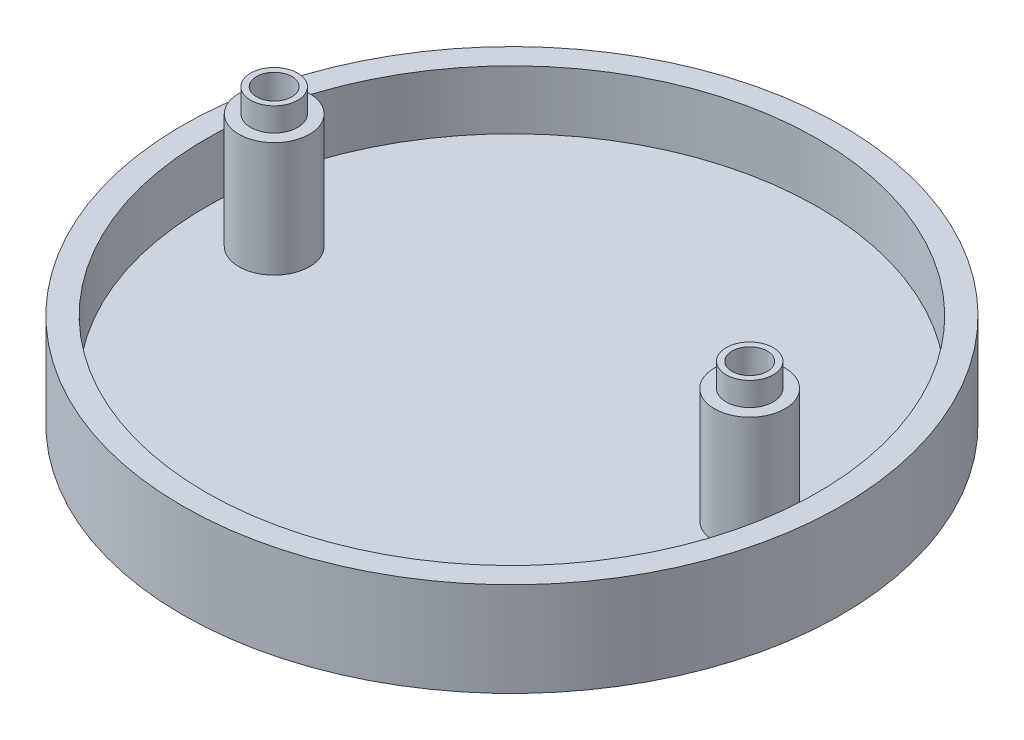
SolidWorks part; units mm, degrees
ref_plane "Front Plane" through (0, 0, 0) normal (0, 0, 1) x (1, 0, 0)
ref_plane "Top Plane" through (0, 0, 0) normal (0, 1, 0) x (1, 0, 0)
ref_plane "Right Plane" through (0, 0, 0) normal (1, 0, 0) x (0, 0, -1)
sketch "Sketch1" plane through (0, 0, 0) normal (0, 1, 0) x (1, 0, 0)
  circle A0 centre (0, 0) radius 28
  circle A1 centre (0, 0) radius 26
  dimension "D1" = 56
  dimension "D2" = 52
extrude "Boss-Extrude1" add sketch "Sketch1" along normal blind 8
sketch "Sketch3" plane through (0, 0, 0) normal (0, 1, 0) x (1, 0, 0)
  circle A0 centre (0, 0) radius 24
extrude "Boss-Extrude2" add sketch "Sketch3" along normal blind 3
sketch "Sketch5" plane through (0, 3, 0) normal (0, 1, 0) x (1, 0, 0)
  line L0 (0, 0) -> (-20.2, 0) construction
  line L1 (0, -4.4) -> (0, 4.4) construction
  circle A0 centre (-20.2, 0) radius 2
  circle A1 centre (20.2, 0) radius 2
  dimension "D2" = 4
  dimension "D1" = 20.2
extrude "Boss-Extrude3" add sketch "Sketch5" along normal blind 11.75 and the other way blind 2.5
sketch "Sketch10" plane through (0, 0, 0) normal (0, -1, 0) x (-1, 0, 0)
  circle A0 centre (0, 0) radius 28
extrude "Boss-Extrude4" add sketch "Sketch10" against normal up to surface (3 mm away) up to face at (0, 3, 24)
sketch "Sketch16" plane through (0, 3, 0) normal (0, 1, 0) x (1, 0, 0)
  line L0 (0, -4.4) -> (0, 4.4) construction
  circle A0 centre (20.2, 0) radius 3
  circle A1 centre (-20.2, 0) radius 3
extrude "Boss-Extrude5" add sketch "Sketch16" along normal blind 9.75
sketch "Sketch20" plane through (0, 14.75, 0) normal (0, 1, 0) x (1, 0, 0)
  line L0 (0, -8.1125) -> (0, 8.1125) construction
  circle A0 centre (20.2, 0) radius 1.5
  circle A1 centre (-20.2, 0) radius 1.5
  dimension "D1" = 3
extrude "Cut-Extrude2" cut sketch "Sketch20" against normal blind 30
sketch "Sketch21" plane through (0, 0, 0) normal (0, -1, 0) x (1, 0, 0)
  line L0 (0, -8.1125) -> (0, 8.1125) construction
  circle A0 centre (20.2, 0) radius 2.5
  circle A1 centre (-20.2, 0) radius 2.5
  dimension "D1" = 5
extrude "Cut-Extrude3" cut sketch "Sketch21" against normal blind 1 contours A1 | A0
